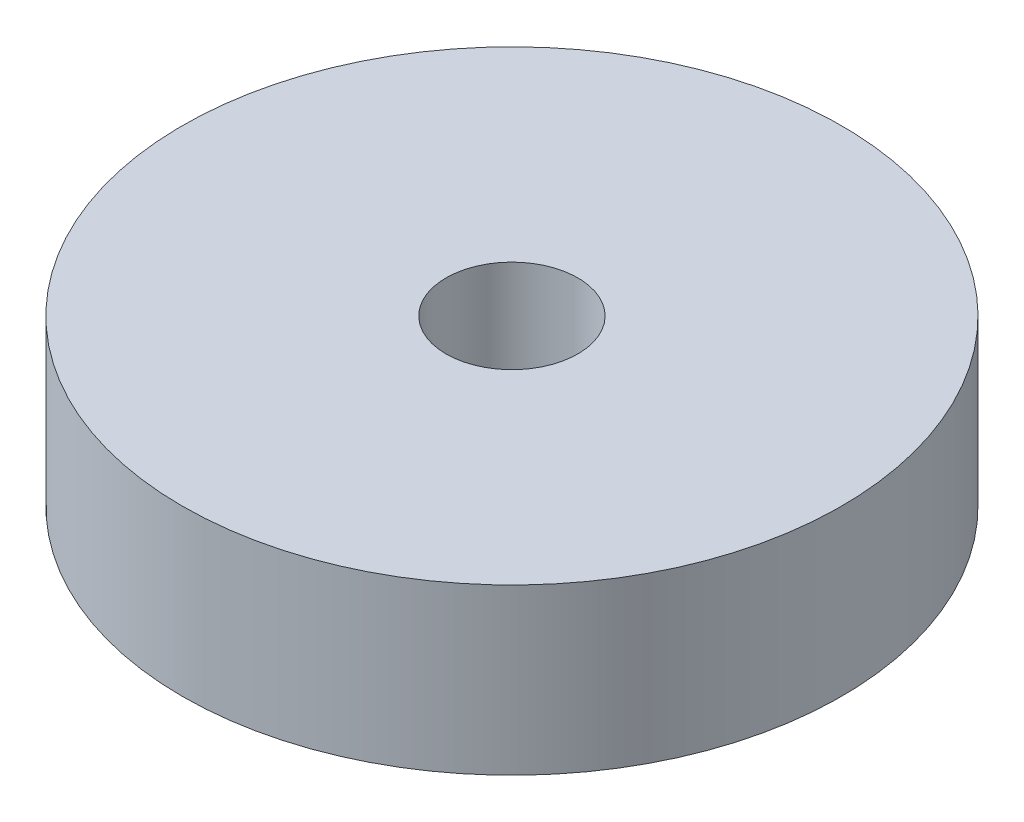
SolidWorks part; units mm, degrees
ref_plane "Front Plane" through (0, 0, 0) normal (0, 0, 1) x (1, 0, 0)
ref_plane "Top Plane" through (0, 0, 0) normal (0, 1, 0) x (1, 0, 0)
ref_plane "Right Plane" through (0, 0, 0) normal (1, 0, 0) x (0, 0, -1)
sketch "Sketch1" plane through (0, 0, 0) normal (0, 1, 0) x (1, 0, 0)
  circle A0 centre (0, 0) radius 20
  circle A1 centre (0, 0) radius 4
  dimension "D1" = 8
  dimension "D2" = 40
extrude "Boss-Extrude1" add sketch "Sketch1" along normal blind 10
sketch "Sketch3" plane through (0, 0, 0) normal (0, 1, 0) x (1, 0, 0)
  line L5 (-12, 3.3205) -> (-12, -3.3205)
  line L6 (-18, 3.3205) -> (-18, -3.3205)
  arc A3 (-18, 3.3205) -> (-12, 3.3205) centre (-15, 0) cw
  arc A4 (-18, -3.3205) -> (-12, -3.3205) centre (-15, 0) ccw
  dimension "D3" = 15
  dimension "D2" = 4.475
  dimension "D1" = 6
extrude "Cut-Extrude1" cut sketch "Sketch3" along normal blind 7
ref_plane "Plane1" through (-18, 0, 0) normal (1, 0, 0) x (0, 0, -1)
sketch "Sketch4" plane through (-18, 0, 0) normal (1, 0, 0) x (0, 0, -1)
  line L0 (3.3205, 0) -> (-3.3205, 0) construction
  circle A0 centre (0, 3) radius 2.125
  dimension "D1" = 3
  dimension "D2" = 4.25
extrude "Cut-Extrude2" cut sketch "Sketch4" against normal through all
